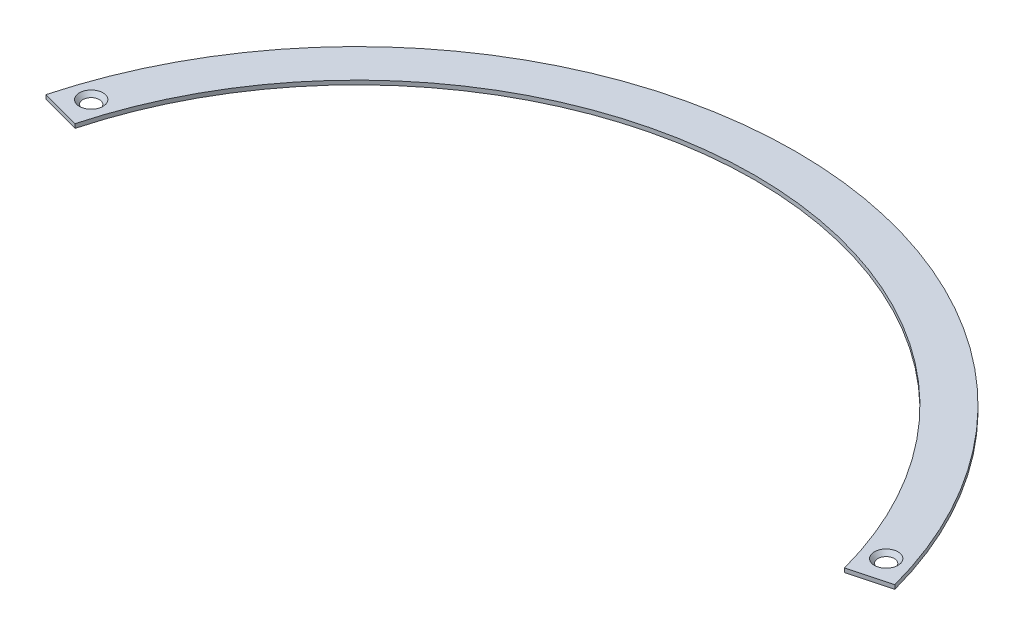
SolidWorks part; units mm, degrees
material "AISI 304"
ref_plane "Front Plane" through (0, 0, 0) normal (0, 0, 1) x (1, 0, 0)
ref_plane "Top Plane" through (0, 0, 0) normal (0, 1, 0) x (1, 0, 0)
ref_plane "Right Plane" through (0, 0, 0) normal (1, 0, 0) x (0, 0, -1)
sketch "Sketch2" plane through (0, 0, 0) normal (0, 1, 0) x (1, 0, 0)
  line L0 (-148.7405, 39.8549) -> (-164.0746, 43.9637)
  line L1 (164.0746, 43.9637) -> (148.7405, 39.8549)
  arc A0 (-148.7405, 39.8549) -> (148.7405, 39.8549) centre (0, 0) cw
  arc A1 (164.0746, 43.9637) -> (-164.0746, 43.9637) centre (0, 0) ccw
  point P7 (0, 153.9875)
  dimension "D1" = 150
  dimension "D2" = 169.8625
  dimension "D3" = 15.875
extrude "Boss-Extrude1" add sketch "Sketch2" along normal blind 1.5875
hole_wizard "CSK for #8 Flat Head Socket Cap Screw1" positions "Sketch3" profile "Sketch4" countersink size "#8" standard "ANSI Inch" end condition through all
sketch "Sketch3" plane through (0, 1.5875, 0) normal (0, 1, 0) x (1, 0, 0)
  line L0 (148.7405, 39.8549) -> (164.0746, 43.9637) construction
  line L1 (-164.0746, 43.9637) -> (-148.7405, 39.8549) construction
  arc A0 (156.4075, 41.9093) -> (153.6728, 51.0332) centre (0, 0) ccw
  arc A1 (-156.4075, 41.9093) -> (-153.6728, 51.0332) centre (0, 0) cw
  point P0 (-153.6728, 51.0332)
  point P2 (153.6728, 51.0332)
  dimension "D1" = 9.525
sketch "Sketch4" plane through (-153.6728, 1.5875, -51.0332) normal (1, 0, 0) x (0, 0, 1)
  line L0 (0, 0) -> (0, 1.5875)
  line L1 (0, 1.5875) -> (2.2479, 1.5875)
  line L2 (2.2479, 1.5875) -> (2.2479, 2.659)
  line L3 (2.2479, 2.659) -> (4.5593, 0)
  line L5 (4.5593, 0) -> (0, 0)
  line L6 (-2.2479, 2.659) -> (-4.5593, 0) construction
  line L11 (0, -6.35) -> (0, 107.95) construction
  dimension "Thru Hole Dia." = 4.4958
  dimension "Thru Hole Depth" = 1.5875
  dimension "Near C'Sink Dia." = 9.1186
  dimension "Near C'Sink Angle" = 82
